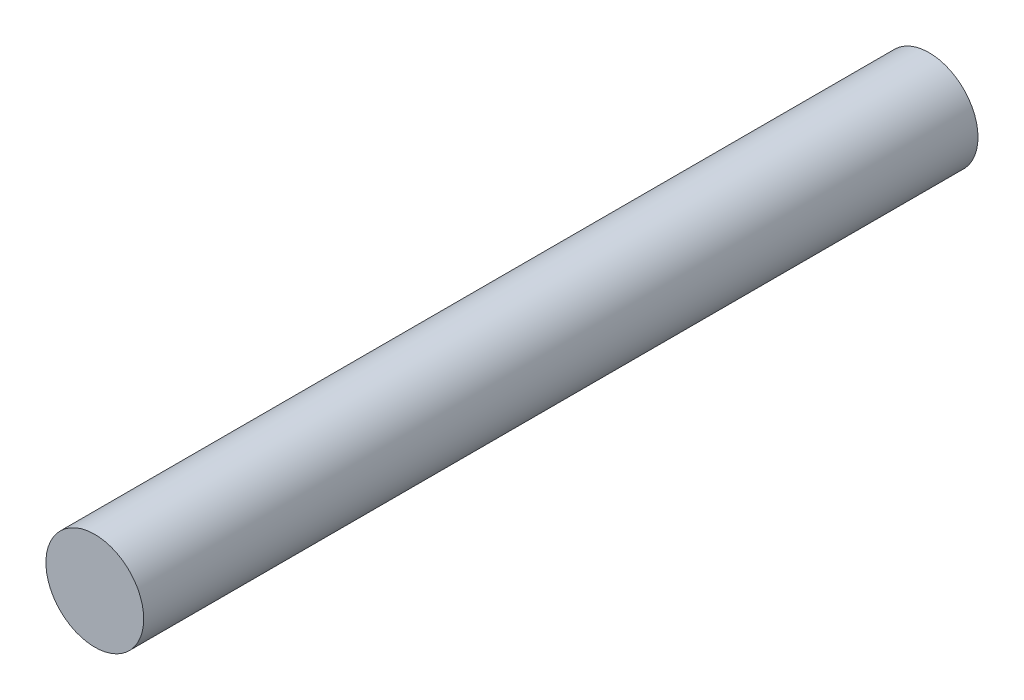
SolidWorks part; units mm, degrees
ref_plane "Front Plane" through (0, 0, 0) normal (0, 0, 1) x (1, 0, 0)
ref_plane "Top Plane" through (0, 0, 0) normal (0, 1, 0) x (1, 0, 0)
ref_plane "Right Plane" through (0, 0, 0) normal (1, 0, 0) x (0, 0, -1)
sketch "Sketch1" plane through (0, 0, 0) normal (0, 0, 1) x (1, 0, 0)
  circle A0 centre (0, 0) radius 1
extrude "Boss-Extrude1" add sketch "Sketch1" along normal blind 17.0674
